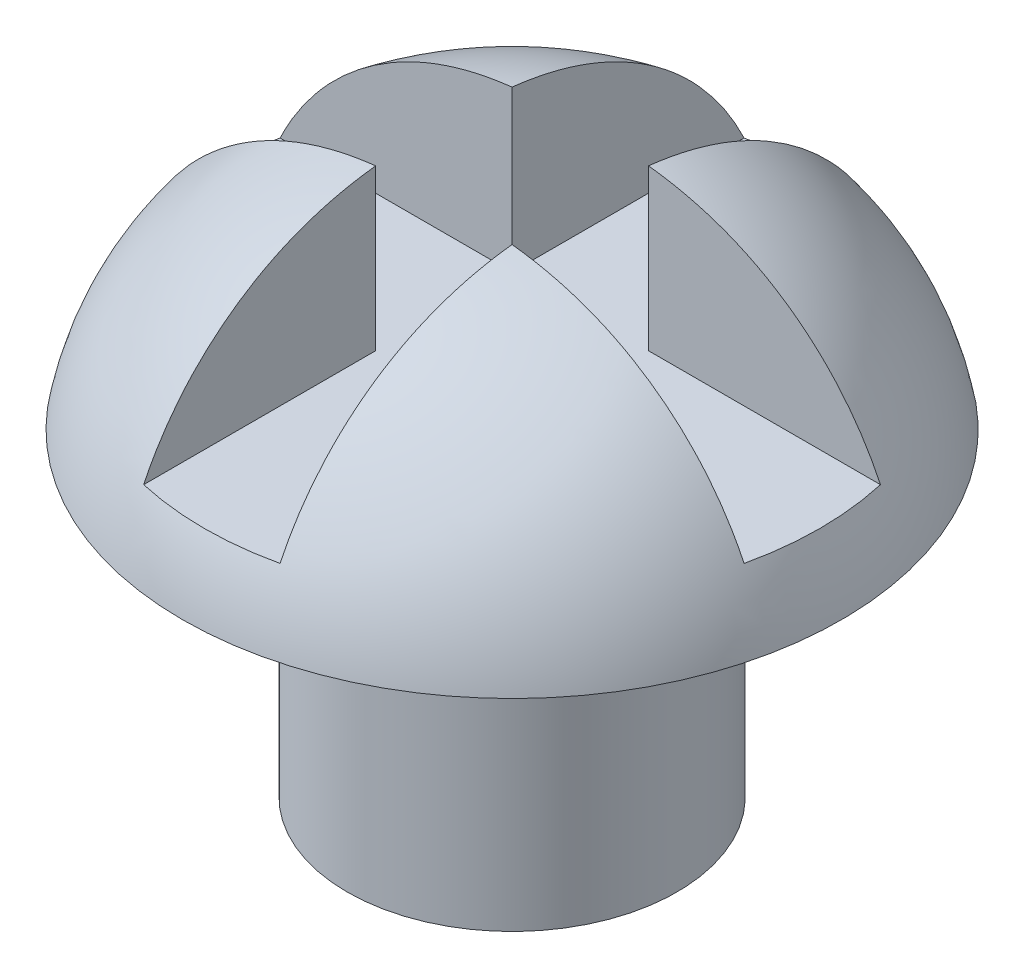
SolidWorks part; units mm, degrees
ref_plane "Front Plane" through (0, 0, 0) normal (0, 0, 1) x (1, 0, 0)
ref_plane "Top Plane" through (0, 0, 0) normal (0, 1, 0) x (1, 0, 0)
ref_plane "Right Plane" through (0, 0, 0) normal (1, 0, 0) x (0, 0, -1)
sketch "Sketch1" plane through (0, 0, 0) normal (0, 0, 1) x (1, 0, 0)
  line L0 (0, 23.8331) -> (0, -27.8832) construction
  line L1 (0, 0) -> (3.683, 0)
  line L2 (0, 0) -> (0, 2.54)
  arc A0 (0, 2.54) -> (3.683, 0) centre (0.5715, -0.5715) cw
  dimension "D1" = 3.683
revolve "Revolve1" add sketch "Sketch1" angle 360 about L0
ref_plane "Plane1" through (0, 3.81, 0) normal (0, -1, 0) x (-1, 0, 0)
sketch "Sketch2" plane through (0, 3.81, 0) normal (0, -1, 0) x (-1, 0, 0)
  line L0 (-0.762, -0.762) -> (-0.762, -3.9583)
  line L1 (0.762, 0.762) -> (5.5041, 0.762)
  line L2 (-0.762, 3.9721) -> (-0.762, 0.762)
  line L3 (0.762, 3.9721) -> (0.762, 0.762)
  line L4 (-5.0605, -0.762) -> (-0.762, -0.762)
  line L5 (-5.0605, 0.762) -> (-0.762, 0.762)
  line L6 (-5.0605, 0.762) -> (-5.0605, -0.762)
  line L7 (5.5041, 0.762) -> (5.5041, -0.762)
  line L8 (0.762, -3.9583) -> (-0.762, -3.9583)
  line L9 (-0.762, 3.9721) -> (0.762, 3.9721)
  line L10 (0.762, -0.762) -> (0.762, -3.9583)
  line L11 (0.762, -0.762) -> (5.5041, -0.762)
extrude "Cut-Extrude1" cut sketch "Sketch2" along normal blind 3.048
sketch "Sketch3" plane through (0, 0, 0) normal (0, -1, 0) x (1, 0, 0)
  circle A0 centre (0, 0) radius 1.8427
extrude "Boss-Extrude1" add sketch "Sketch3" along normal blind 3.556
